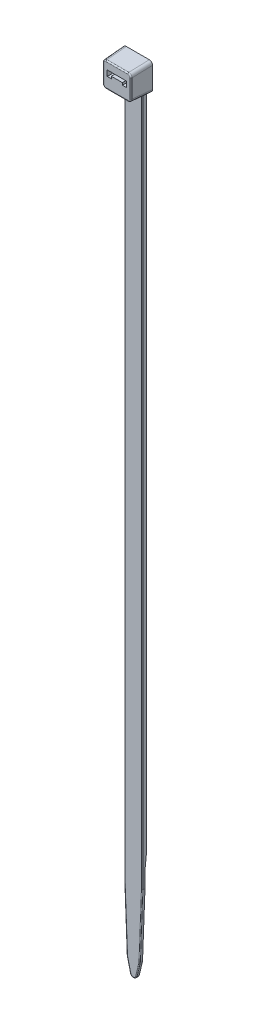
SolidWorks part; units mm, degrees
ref_plane "Front Plane" through (0, 0, 0) normal (0, 0, 1) x (1, 0, 0)
ref_plane "Top Plane" through (0, 0, 0) normal (0, 1, 0) x (1, 0, 0)
ref_plane "Right Plane" through (0, 0, 0) normal (1, 0, 0) x (0, 0, -1)
sketch "Sketch1" plane through (0, 0, 0) normal (1, 0, 0) x (0, 0, -1)
  line L0 (-5.2, -3.4) -> (5.2005, -3.4) construction
  line L1 (0, 0) -> (-5.2, -0.325)
  line L2 (-5.2, -0.325) -> (-5.2, -6.475)
  line L3 (-5.2, -6.475) -> (-1.13, -6.7294)
  line L4 (-1.13, -6.7294) -> (-1.13, -198.5)
  line L5 (-1.13, -198.5) -> (-0.43, -198.5)
  line L6 (-0.43, -198.5) -> (-0.43, -174.5)
  line L7 (-0.43, -174.5) -> (0, -170.5)
  line L8 (0, -170.5) -> (0, 0)
  point P11 (0, -6.8)
  dimension "D1" = 1.13
  dimension "D2" = 6.8
  dimension "D3" = 5.2
  dimension "D4" = 6.15
  dimension "D5" = 0.7
  dimension "D6" = 24
  dimension "D7" = 4
  dimension "D8" = 198.5
extrude "Boss-Extrude1" add sketch "Sketch1" along normal mid plane 4.43
sketch "Sketch2" plane through (0, 0, 0) normal (0, 1, 0) x (1, 0, 0)
  line L0 (-3.66, 0) -> (3.66, 0)
  line L1 (3.66, 0) -> (3.5, -5.2)
  line L2 (3.5, -5.2) -> (-3.5, -5.2)
  line L4 (0, 0) -> (0, -8.1285) construction
  line L5 (2.215, -5.2) -> (-2.215, -5.2) construction
  line L6 (-3.66, 0) -> (-3.5, -5.2)
  dimension "D1" = 7.32
  dimension "D2" = 7
extrude "Boss-Extrude3" add sketch "Sketch2" against normal up to surface and the other way up to surface from offset 1 contours L0 L1 L2 L6 up to face at (0, -6.6022, 3.165) other way up to face at (0, -0.1625, 2.6) offset against normal yes
sketch "Sketch3" plane through (0, 0, 5.2) normal (0, 0, 1) x (1, 0, 0)
  line L0 (-2.4, -2.225) -> (2.4, -2.225)
  line L1 (3.5, -0.325) -> (-3.5, -0.325) construction
  line L2 (2.4, -2.225) -> (2.4, -3.625)
  line L3 (2.4, -3.625) -> (1.375, -3.625)
  line L4 (0, 0) -> (0, -9.9889) construction
  line L5 (1.375, -3.625) -> (1.375, -3.075)
  line L6 (1.375, -3.075) -> (-1.375, -3.075)
  line L7 (-2.4, -2.225) -> (-2.4, -3.625)
  line L8 (-1.375, -3.625) -> (-1.375, -3.075)
  line L9 (-2.4, -3.625) -> (-1.375, -3.625)
  dimension "D1" = 1.9
  dimension "D2" = 1.4
  dimension "D3" = 4.8
  dimension "D4" = 0.85
  dimension "D5" = 2.75
extrude "Cut-Extrude1" cut sketch "Sketch3" against normal up to surface (5.2 mm away) up to face at (0, -46.025, 0)
sketch "Sketch5" plane through (0, 0, 1.13) normal (0, 0, 1) x (1, 0, 0)
  line L0 (0, 0) -> (0, -209.4219) construction
  line L2 (2.215, -198.5) -> (-2.215, -198.5) construction
  line L3 (0.7774, -197.8887) -> (1.6, -194.5)
  line L4 (1.6, -194.5) -> (2.215, -178.5)
  line L5 (2.215, -6.7294) -> (2.215, -198.5) construction
  line L6 (2.215, -178.5) -> (2.215, -198.6)
  line L7 (2.215, -198.6) -> (-2.215, -198.6)
  line L8 (-1.6, -194.5) -> (-2.215, -178.5)
  line L9 (-0.7774, -197.8887) -> (-1.6, -194.5)
  line L10 (-2.215, -178.5) -> (-2.215, -198.6)
  arc A0 (-0.7774, -197.8887) -> (0.7774, -197.8887) centre (0, -197.7) ccw
  dimension "D1" = 0.8
  dimension "D2" = 20
  dimension "D3" = 4
  dimension "D4" = 3.2
  dimension "D5" = 0.1
extrude "Cut-Extrude2" cut sketch "Sketch5" against normal up to surface (0.7 mm away) up to face at (0, -186.5, 0.43)
fillet "Fillet1" radius 2 4 edges at (-1.6, -194.5, 0.78) (1.6, -194.5, 0.78) (-2.215, -178.5, 0.78) (2.215, -178.5, 0.78)
fillet "Fillet2" radius 0.8 4 edges at (3.58, -0.1625, 2.6) (3.58, -6.6375, 2.6) (-3.58, -0.1625, 2.6) (-3.58, -6.6375, 2.6)
fillet "Fillet4" radius 0.2 11 edges at (-2.215, -92.5955, 1.13) (2.215, -92.5955, 1.13) (-2.2146, -178.5, 1.13) (-1.9106, -186.4191, 1.13) (-1.5901, -194.4986, 1.13) (-1.1651, -196.2917, 1.13) (0, -198.5, 1.13) (1.1651, -196.2917, 1.13) (1.5901, -194.4986, 1.13) (1.9106, -186.4191, 1.13) (2.2146, -178.5, 1.13)
fillet "Fillet3" radius 0.5 5 edges at (2.215, -6.7709, 0.465) (-2.215, -6.7709, 0.465) (-2.1564, -6.733, 1.0714) (0, -6.7294, 1.13) (2.1564, -6.733, 1.0714)
fillet "Fillet5" radius 0.3 8 edges at (3.2661, -6.2408, 5.2) (0, -6.475, 5.2) (-3.2661, -6.2408, 5.2) (-3.5, -3.4, 5.2) (-3.2661, -0.5592, 5.2) (0, -0.325, 5.2) (3.2661, -0.5592, 5.2) (3.5, -3.4, 5.2)
